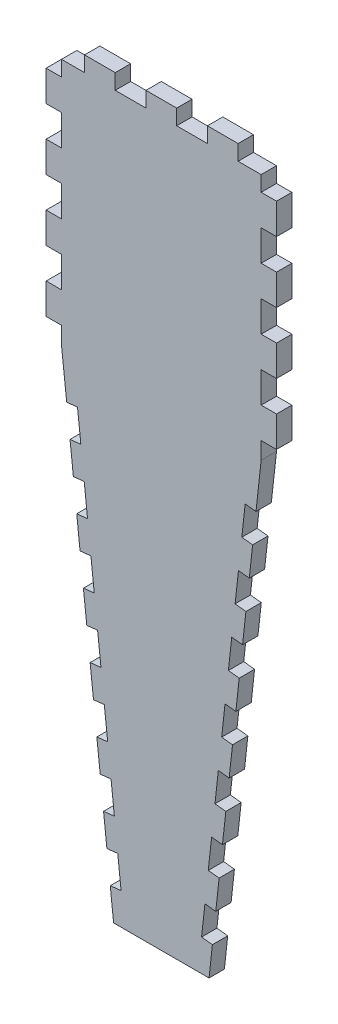
SolidWorks part; units mm, degrees
material "Pine"
ref_plane "Front Plane" through (0, 0, 0) normal (0, 0, 1) x (1, 0, 0)
ref_plane "Top Plane" through (0, 0, 0) normal (0, 1, 0) x (1, 0, 0)
ref_plane "Right Plane" through (0, 0, 0) normal (1, 0, 0) x (0, 0, -1)
sketch "Sketch1" plane through (0, 0, 0) normal (0, 0, 1) x (1, 0, 0)
  line L1 (0, 0) -> (95.25, 0)
  line L2 (0, 0) -> (0, 304.8)
  line L3 (0, 304.8) -> (95.25, 304.8)
  line L4 (95.25, 0) -> (95.25, 304.8)
  dimension "D1" = 95.25
  dimension "D2" = 304.8
extrude "Boss-Extrude1" add sketch "Sketch1" along normal blind 6.35
sketch "Sketch2" plane through (0, 0, 6.35) normal (0, 0, 1) x (1, 0, 0)
  line L0 (0, 254) -> (27.8981, 0)
  line L1 (0, 304.8) -> (0, 0) construction
  line L2 (0, 0) -> (95.25, 0) construction
  line L3 (0, 254) -> (0, 0)
  line L4 (0, 0) -> (27.8981, 0)
  line L5 (67.3519, 0) -> (95.25, 0)
  line L6 (95.25, 0) -> (95.25, 254)
  line L7 (95.25, 0) -> (95.25, 304.8) construction
  line L8 (95.25, 254) -> (67.3519, 0)
  line L9 (95.25, 254) -> (0, 254) construction
  line L11 (27.8981, 0) -> (67.3519, 0) construction
  line L12 (67.3519, 0) -> (95.25, 27.8981) construction
  line L13 (95.25, 27.8981) -> (95.25, 67.3519) construction
  line L14 (95.25, 67.3519) -> (67.3519, 95.25) construction
  line L15 (67.3519, 95.25) -> (27.8981, 95.25) construction
  line L16 (27.8981, 95.25) -> (0, 67.3519) construction
  line L17 (0, 67.3519) -> (0, 27.8981) construction
  line L18 (0, 27.8981) -> (27.8981, 0) construction
  circle A0 centre (47.625, 47.625) radius 47.625 construction
  dimension "D1" = 254
  dimension "D2" = 95.25
extrude "Cut-Extrude1" cut sketch "Sketch2" against normal through all
sketch "Sketch3" plane through (0, 0, 6.35) normal (0, 0, 1) x (1, 0, 0)
  line L1 (0, 304.8) -> (6.35, 304.8)
  line L2 (0, 304.8) -> (0, 292.1)
  line L3 (0, 292.1) -> (6.35, 292.1)
  line L4 (6.35, 304.8) -> (6.35, 292.1)
  line L5 (95.25, 304.8) -> (88.9, 304.8)
  line L6 (95.25, 304.8) -> (95.25, 292.1)
  line L7 (95.25, 292.1) -> (88.9, 292.1)
  line L8 (88.9, 304.8) -> (88.9, 292.1)
  dimension "D1" = 12.7
  dimension "D2" = 6.35
extrude "Cut-Extrude2" cut sketch "Sketch3" against normal through all
sketch "Sketch4" plane through (0, 0, 6.35) normal (0, 0, 1) x (1, 0, 0)
  line L0 (88.9, 304.8) -> (6.35, 304.8) construction
  line L1 (6.35, 304.8) -> (15.875, 304.8)
  line L2 (6.35, 304.8) -> (6.35, 298.45)
  line L3 (6.35, 298.45) -> (15.875, 298.45)
  line L4 (15.875, 304.8) -> (15.875, 298.45)
  line L5 (28.575, 304.8) -> (41.275, 304.8)
  line L6 (28.575, 304.8) -> (28.575, 298.45)
  line L7 (28.575, 298.45) -> (41.275, 298.45)
  line L8 (41.275, 304.8) -> (41.275, 298.45)
  line L10 (53.975, 304.8) -> (66.675, 304.8)
  line L11 (53.975, 304.8) -> (53.975, 298.45)
  line L12 (53.975, 298.45) -> (66.675, 298.45)
  line L13 (66.675, 304.8) -> (66.675, 298.45)
  line L14 (88.9, 304.8) -> (79.375, 304.8)
  line L15 (88.9, 304.8) -> (88.9, 298.45)
  line L16 (88.9, 298.45) -> (79.375, 298.45)
  line L17 (79.375, 304.8) -> (79.375, 298.45)
  dimension "D1" = 12.7
  dimension "D2" = 6.35
  dimension "D3" = 12.7
  dimension "D4" = 12.7
  dimension "D5" = 12.7
extrude "Cut-Extrude3" cut sketch "Sketch4" against normal through all
sketch3d "3DSketch1"
  line L0 (0, 254, 6.35) -> (0, 25.2482, 6.35) construction
  line L1 (0, 25.2482, 6.35) -> (25.1249, 25.2482, 6.35) construction
  line L2 (27.8981, 0, 6.35) -> (0, 254, 6.35) construction
  line L3 (0, 25.2482, 6.35) -> (0, 25.2482, -18.7749) construction
  line L4 (25.1249, 25.2482, 6.35) -> (0, 25.2482, -18.7749) construction
  line L5 (0, 25.2482, -18.7749) -> (1.3866, 12.6241, -18.7749) construction
  line L6 (1.3866, 12.6241, -18.7749) -> (26.5115, 12.6241, 6.35) construction
  line L7 (26.5115, 12.6241, 6.35) -> (25.1249, 25.2482, 6.35) construction
  line L8 (26.5115, 12.6241, 6.35) -> (30.9882, 13.1158, 1.8734) construction
  dimension "D1" = 12.7
  dimension "D2" = 12.7
  dimension "D3" = 6.35
sketch "Sketch5" plane through (0, 0, 6.35) normal (0, 0, 1) x (1, 0, 0)
  line L0 (26.5115, 12.6241) -> (25.1249, 25.2482)
  line L1 (26.5115, 12.6241) -> (30.9882, 13.1158)
  line L3 (30.9882, 13.1158) -> (29.6016, 25.7399)
  line L4 (27.8981, 0) -> (0, 254) construction
  line L5 (25.1249, 25.2482) -> (29.6016, 25.7399)
  dimension "D1" = 12.7
  dimension "D3" = 12.7
extrude "Cut-Extrude4" cut sketch "Sketch5" against normal through all
pattern_linear "LPattern2" count 7 spacing 25.4 along (-0.1092, 0.994, 0) of "Cut-Extrude4"
sketch "Sketch6" plane through (0, 0, 6.35) normal (0, 0, 1) x (1, 0, 0)
  line L0 (68.7385, 12.6241) -> (70.1251, 25.2482)
  line L1 (68.7385, 12.6241) -> (64.2618, 13.1158)
  line L2 (70.1251, 25.2482) -> (65.6484, 25.7399)
  line L3 (64.2618, 13.1158) -> (65.6484, 25.7399)
  line L4 (95.25, 254) -> (67.3519, 0) construction
  line L5 (26.5115, 12.6241) -> (30.9882, 13.1158) construction
  line L6 (30.9882, 13.1158) -> (29.6016, 25.7399) construction
  dimension "D1" = 12.7
extrude "Cut-Extrude5" cut sketch "Sketch6" against normal through all
pattern_linear "LPattern3" count 7 spacing 25.4 along (0.1092, 0.994, 0) of "Cut-Extrude5"
sketch "Sketch9" plane through (0, 0, 6.35) normal (0, 0, 1) x (1, 0, 0)
  line L0 (8.4862, 176.7371) -> (0, 254) construction
  line L1 (0, 254) -> (6.35, 254)
  line L2 (0, 254) -> (0, 196.186)
  line L3 (0, 196.186) -> (6.35, 196.186)
  line L4 (6.35, 254) -> (6.35, 196.186)
  line L5 (95.25, 254) -> (86.7638, 176.7371) construction
  line L6 (95.25, 254) -> (88.9, 254)
  line L7 (95.25, 254) -> (95.25, 196.186)
  line L8 (95.25, 196.186) -> (88.9, 196.186)
  line L9 (88.9, 254) -> (88.9, 196.186)
  line L10 (6.35, 292.1) -> (6.35, 298.45) construction
extrude "Boss-Extrude2" add sketch "Sketch9" against normal through all
pattern_linear "LPattern4" count 5 spacing 25.4 along (0, -1, 0) of "Cut-Extrude2"
